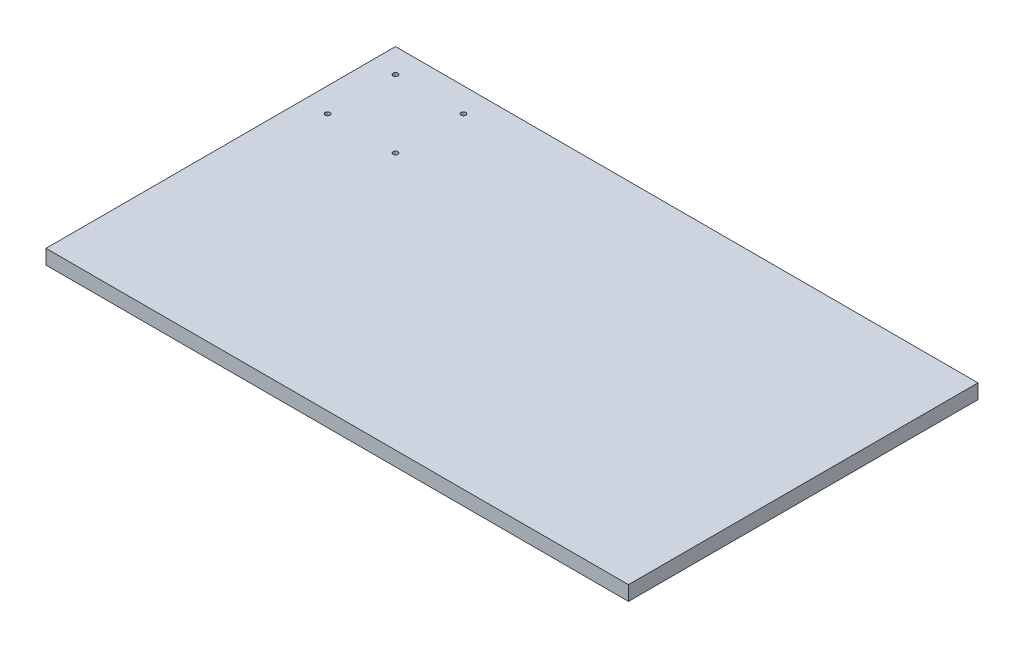
SolidWorks part; units mm, degrees
material "Plain Carbon Steel"
ref_plane "Front Plane" through (0, 0, 0) normal (0, 0, 1) x (1, 0, 0)
ref_plane "Top Plane" through (0, 0, 0) normal (0, 1, 0) x (1, 0, 0)
ref_plane "Right Plane" through (0, 0, 0) normal (1, 0, 0) x (0, 0, -1)
sketch "Sketch1" plane through (0, 0, 0) normal (0, 1, 0) x (1, 0, 0)
  line L1 (0, 0) -> (3048, 0)
  line L2 (0, 0) -> (0, 1828.8)
  line L3 (0, 1828.8) -> (3048, 1828.8)
  line L4 (3048, 0) -> (3048, 1828.8)
  dimension "D1" = 3048
  dimension "D2" = 1828.8
extrude "Boss-Extrude1" add sketch "Sketch1" along normal blind 76.2
sketch "Sketch2" plane through (0, 0, 0) normal (0, -1, 0) x (1, 0, 0)
  line L0 (0, -1828.8) -> (0, 0) construction
  line L1 (76.2, -76.2) -> (2971.8, -76.2)
  line L2 (76.2, -76.2) -> (76.2, -1752.6)
  line L3 (76.2, -1752.6) -> (2971.8, -1752.6)
  line L4 (2971.8, -76.2) -> (2971.8, -1752.6)
  line L5 (0, 0) -> (3048, 0) construction
  line L6 (3048, 0) -> (3048, -1828.8) construction
  line L7 (3048, -1828.8) -> (0, -1828.8) construction
  dimension "D1" = 76.2
  dimension "D2" = 76.2
  dimension "D3" = 76.2
  dimension "D4" = 76.2
extrude "Cut-Extrude1" cut sketch "Sketch2" against normal blind 50.8
sketch "Sketch3" plane through (0, 76.2, 0) normal (0, 1, 0) x (1, 0, 0)
  line L0 (3048, 1828.8) -> (0, 1828.8) construction
  line L1 (0, 1828.8) -> (0, 0) construction
  circle A0 centre (127, 1701.8) radius 12.7
  dimension "D1" = 25.4
  dimension "D2" = 127
  dimension "D3" = 127
extrude "Cut-Extrude2" cut sketch "Sketch3" against normal through all
pattern_linear "LPattern1" count 2 spacing 355.6 along (1, 0, 0) count 2 spacing 355.6 along (0, 0, 1) of "Cut-Extrude2"
